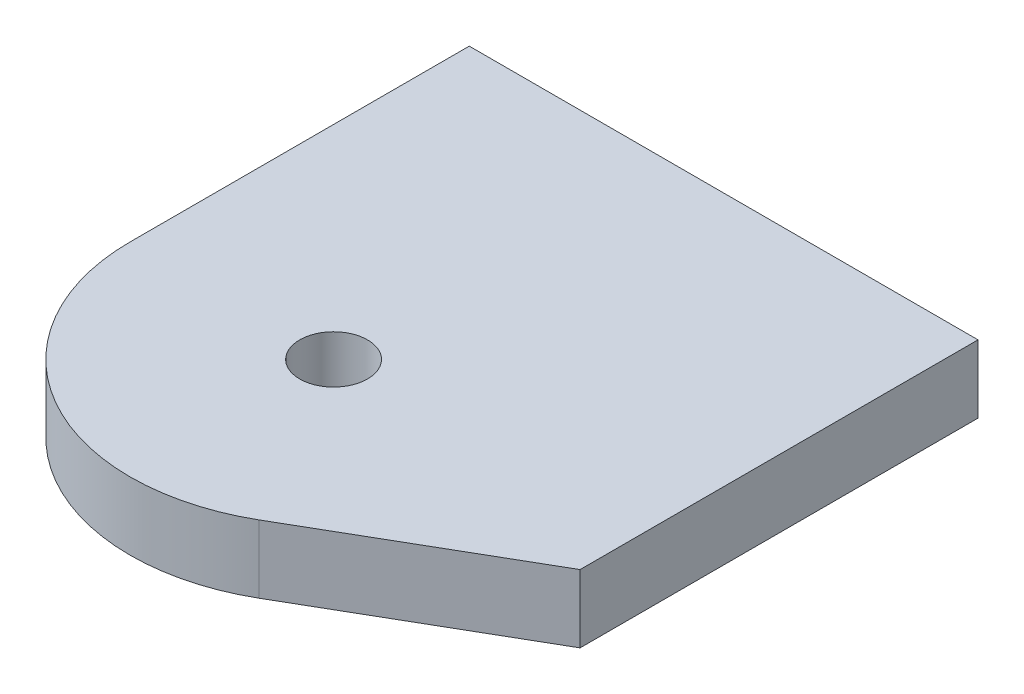
SolidWorks part; units mm, degrees
ref_plane "Plan de face" through (0, 0, 0) normal (0, 0, 1) x (1, 0, 0)
ref_plane "Plan de dessus" through (0, 0, 0) normal (0, 1, 0) x (1, 0, 0)
ref_plane "Plan de droite" through (0, 0, 0) normal (1, 0, 0) x (0, 0, -1)
sketch "Esquisse1" plane through (0, 0, 0) normal (0, 1, 0) x (1, 0, 0)
  line L0 (-6, 0) -> (-6, 10)
  line L1 (-6, 10) -> (9, 10)
  line L2 (3, -5.1962) -> (9, -1.7321)
  line L3 (9, -1.7321) -> (9, 10)
  circle A0 centre (0, 0) radius 1
  arc A1 (-6, 0) -> (3, -5.1962) centre (0, 0) ccw
  dimension "D1" = 2
  dimension "D2" = 6
  dimension "D3" = 120
  dimension "D4" = 10
  dimension "D5" = 15
extrude "Boss.-Extru.1" add sketch "Esquisse1" along normal blind 2
